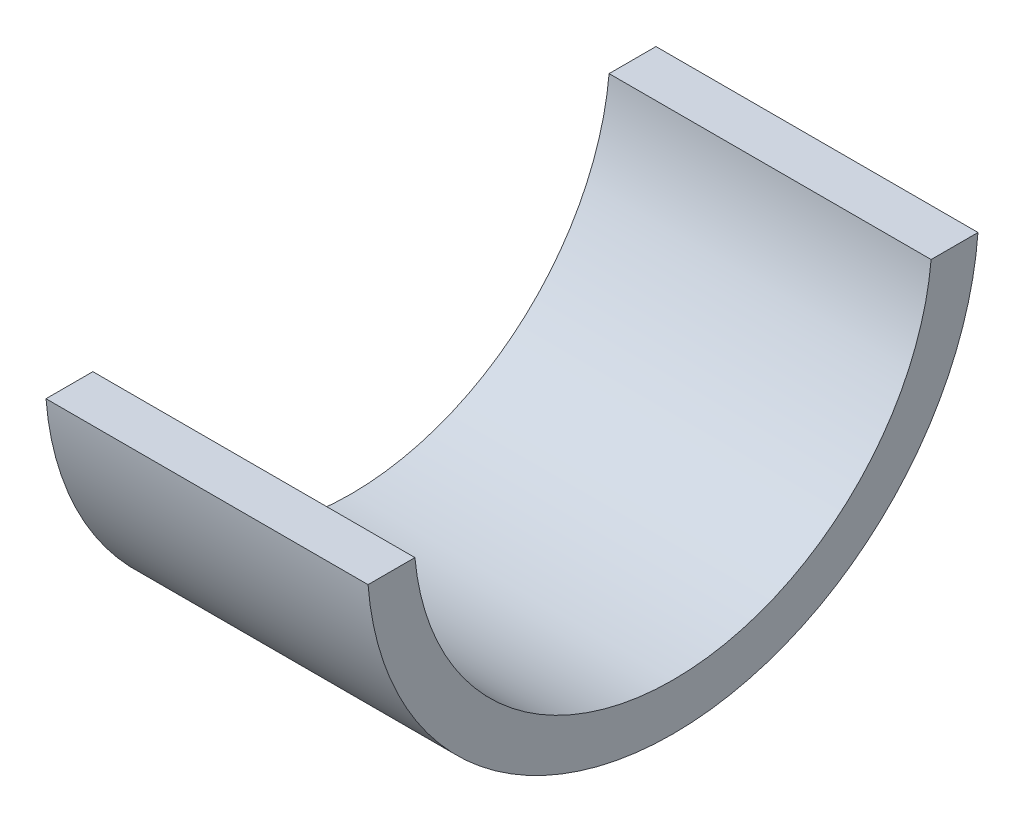
SolidWorks part; units mm, degrees
material "6061-T6 (SS)"
ref_plane "Front Plane" through (0, 0, 0) normal (0, 0, 1) x (1, 0, 0)
ref_plane "Top Plane" through (0, 0, 0) normal (0, 1, 0) x (1, 0, 0)
ref_plane "Right Plane" through (0, 0, 0) normal (1, 0, 0) x (0, 0, -1)
sketch "Sketch1" plane through (0, 0, 0) normal (1, 0, 0) x (0, 0, -1)
  line L0 (-24.0547, -1.905) -> (-20.3581, -1.905)
  line L1 (20.3581, -1.905) -> (24.0547, -1.905)
  arc A0 (-24.0547, -1.905) -> (24.0547, -1.905) centre (0, 0) ccw
  arc A1 (-20.3581, -1.905) -> (20.3581, -1.905) centre (0, 0) ccw
  point P1 (0, -24.13)
  dimension "D1" = 48.26
  dimension "D2" = 22.225
  dimension "D4" = 3.683
extrude "Boss-Extrude1" add sketch "Sketch1" along normal blind 25.4
fillet "Fillet1" [suppressed] radius 9.525
